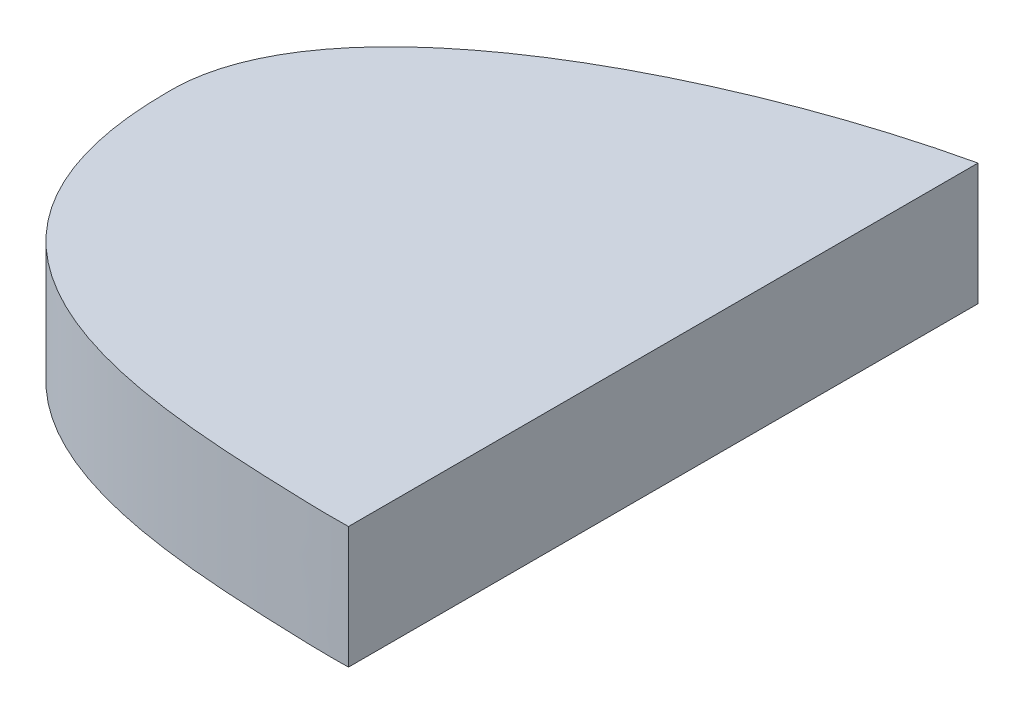
SolidWorks part; units mm, degrees
ref_plane "Front Plane" through (0, 0, 0) normal (0, 0, 1) x (1, 0, 0)
ref_plane "Top Plane" through (0, 0, 0) normal (0, 1, 0) x (1, 0, 0)
ref_plane "Right Plane" through (0, 0, 0) normal (1, 0, 0) x (0, 0, -1)
sketch "Sketch1" plane through (0, 0, 0) normal (0, 1, 0) x (1, 0, 0)
  line L0 (0, 0) -> (0, 15.15) construction
  line L1 (0, 15.15) -> (-100.9, 15.15) construction
  line L2 (-100.9, 15.15) -> (-100.9, -15.15) construction
  line L3 (-100.9, -15.15) -> (10.4, -15.15) construction
  line L4 (10.4, -15.15) -> (10.4, 15.15) construction
  line L5 (10.4, 15.15) -> (0, 15.15) construction
  line L6 (0, 0) -> (10.4, 0) construction
  line L7 (0, 0) -> (-100.9, 0) construction
  line L8 (-3.6, 0) -> (-3.6, 20) construction
  line L9 (10.4, 0) -> (19.6, 0) construction
  line L10 (-59.2, 0) -> (-59.2, 24.5) construction
  line L11 (-64.1, 0) -> (-64.1, 15.15) construction
  line L12 (-64.1, 0) -> (-64.1, -5.1) construction
  line L13 (-64.1, -5.1) -> (-109.1, -5.1) construction
  line L14 (-24.8, 0) -> (-24.8, 17.7) construction
  dimension "D1" = 30.3
  dimension "D2" = 111.3
  dimension "D3" = 10.4
  dimension "D4" = 3.6
  dimension "D5" = 20
  dimension "D6" = 19.6
  dimension "D7" = 24.8
  dimension "D8" = 5.1
  dimension "D9" = 45
  dimension "D10" = 64.1
  dimension "D11" = 24.5
  dimension "D12" = 59.2
  dimension "D13" = 17.7
sketch "Sketch3" plane through (0, 0, 0) normal (0, 1, 0) x (1, 0, 0)
  line L0 (0, 0) -> (0, -19.3) construction
  line L1 (-27.1, 0) -> (-27.1, -17.4) construction
  line L2 (0, 0) -> (-100.9, 0) construction
  line L3 (-72, 0) -> (-72, -28.6) construction
  dimension "D1" = 19.3
  dimension "D2" = 17.4
  dimension "D3" = 28.6
  dimension "D4" = 27.1
  dimension "D5" = 72
sketch "Sketch2" plane through (0, 0, 0) normal (0, 1, 0) x (1, 0, 0)
  line L0 (19.6, -11.1333) -> (19.6, 11.1333) construction
  line L1 (-82.9362, -28.6) -> (-59.2746, -28.6) construction
  line L3 (-38.3758, -17.4) -> (-20.5335, -17.4) construction
  line L4 (-6.8012, -19.3) -> (7.7138, -19.3) construction
  line L5 (-44.6362, 24.5) -> (-71.0994, 24.5) construction
  line L6 (-20.2625, 17.7) -> (-32.3488, 17.7) construction
  line L7 (5.0808, 20) -> (-8.6275, 20) construction
  line L8 (19.6, -12.7653) -> (19.6, 13.2246) construction
  spline S0 degree 3 poles (-109.1, -5.1) (-109.4246, 10.4415) (-73.7876, 25.2227) (-43.0203, 23.9373) (-34.2195, 17.8508) (-19.7454, 17.5568) (-9.8315, 20.0896) (7.1736, 19.9352) (19.6, 14.2893) (19.6, 0) knots 0 0 0 0 0.230584 0.286176 0.525951 0.574149 0.719962 0.76437 1 1 1 1
  spline S1 degree 3 poles (19.6, 0) (19.6, -12.7982) (9.6283, -19.5586) (-8.5374, -19.1352) (-19.7964, -17.3572) (-41.2186, -17.3729) (-58.114, -28.9795) (-85.1554, -28.3277) (-109.1, -26.6433) (-109.1, -5.1) knots 0 0 0 0 0.17462 0.213185 0.36648 0.418282 0.679408 0.740843 1 1 1 1
  point P0 (-59.2, 24.5)
  point P2 (-3.6, 20)
  point P4 (19.6, 0)
  point P6 (-109.1, -5.1)
  point P8 (-24.8, 17.7)
extrude "Boss-Extrude1" add sketch "Sketch2" along normal blind 10
sketch "Sketch4" plane through (0, 10, 0) normal (0, 1, 0) x (1, 0, 0)
  line L1 (-70.7929, 36.6353) -> (29.8255, 36.6353)
  line L2 (-70.7929, 36.6353) -> (-70.7929, -36.8355)
  line L3 (-70.7929, -36.8355) -> (29.8255, -36.8355)
  line L4 (29.8255, 36.6353) -> (29.8255, -36.8355)
extrude "Cut-Extrude1" cut sketch "Sketch4" against normal through all
